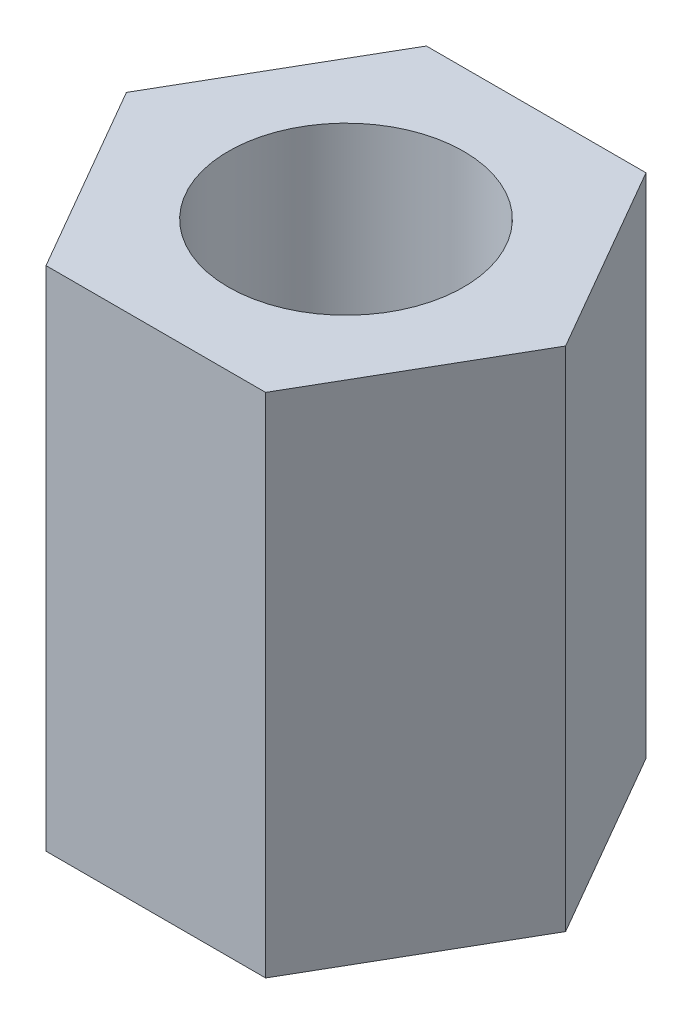
SolidWorks part; units mm, degrees
material "Nylon 6/10"
ref_plane "Front Plane" through (0, 0, 0) normal (0, 0, 1) x (1, 0, 0)
ref_plane "Top Plane" through (0, 0, 0) normal (0, 1, 0) x (1, 0, 0)
ref_plane "Right Plane" through (0, 0, 0) normal (1, 0, 0) x (0, 0, -1)
sketch "Sketch1" plane through (0, 0, 0) normal (0, 1, 0) x (1, 0, 0)
  line L0 (-2.7496, 0) -> (2.7496, 0) construction
  line L1 (-2.7496, 0) -> (-1.3748, 2.3813)
  line L2 (-1.3748, 2.3813) -> (1.3748, 2.3813)
  line L3 (1.3748, 2.3813) -> (2.7496, 0)
  line L4 (2.7496, 0) -> (1.3748, -2.3813)
  line L5 (1.3748, -2.3813) -> (-1.3748, -2.3813)
  line L6 (-1.3748, -2.3813) -> (-2.7496, 0)
  circle A0 centre (0, 0) radius 1.4732
  dimension "D1" = 4.7625
  dimension "D3" = 2.9464
  dimension "D2" = 4.7625
extrude "Boss-Extrude1" add sketch "Sketch1" along normal blind 6.35
